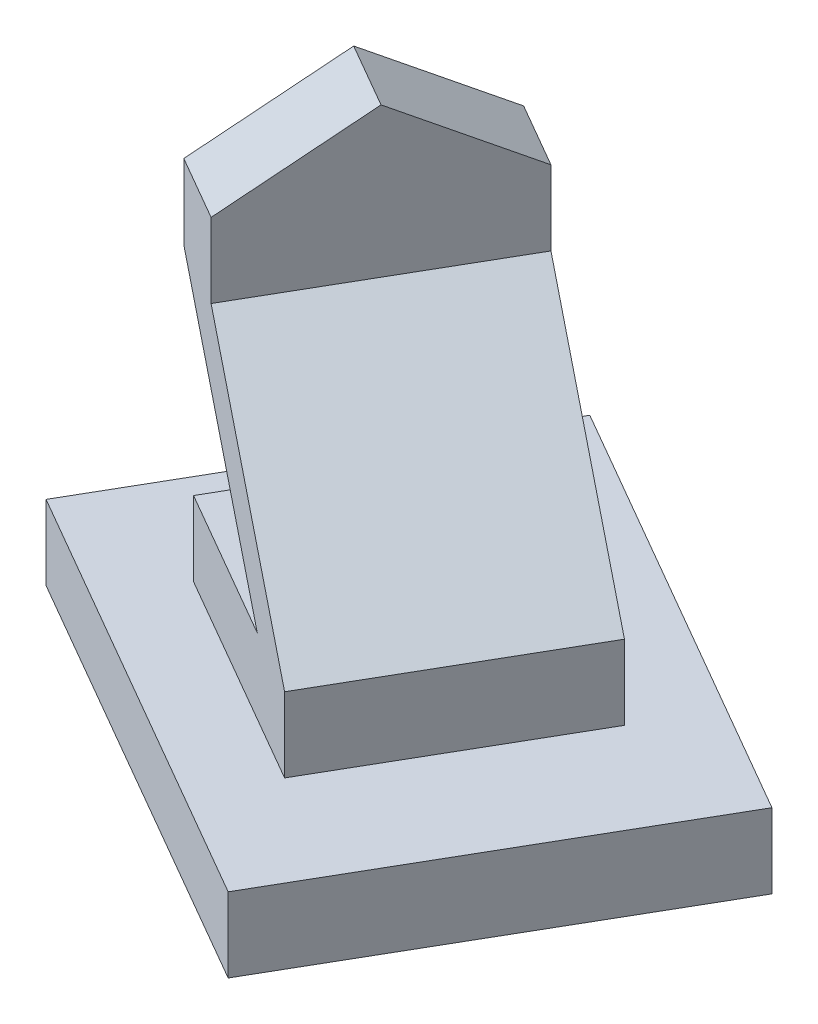
SolidWorks part; units mm, degrees
other "Perspective"
ref_plane "Front" through (0, 0, 0) normal (0, 0, 1) x (1, 0, 0)
ref_plane "Top" through (0, 0, 0) normal (0, 1, 0) x (1, 0, 0)
ref_plane "Right" through (0, 0, 0) normal (1, 0, 0) x (0, 0, -1)
sketch "Sketch1" plane through (0, 0, 0) normal (0, 1, 0) x (1, 0, 0)
  line L0 (0, 0) -> (800, 1385.6406)
  line L1 (800, 1385.6406) -> (-932.0508, 2385.6406)
  line L2 (-932.0508, 2385.6406) -> (-1732.0508, 1000)
  line L3 (-1732.0508, 1000) -> (0, 0)
  line L4 (0, 0) -> (48.1177, 0) construction
  dimension "D1" = 60
  dimension "D2" = 2000
  dimension "D3" = 1600
extrude "Extrude1" add sketch "Sketch1" along normal blind 300
sketch "Sketch2" plane through (0, 300, 0) normal (0, 1, 0) x (-1, 0, 0)
  line L0 (649.0381, -1875.833) -> (-216.9873, -1375.833)
  line L1 (-216.9873, -1375.833) -> (283.0127, -509.8076)
  line L2 (283.0127, -509.8076) -> (1149.0381, -1009.8076)
  line L3 (1149.0381, -1009.8076) -> (649.0381, -1875.833)
  line L4 (1732.0508, -1000) -> (0, 0) construction
  line L5 (932.0508, -2385.6406) -> (1732.0508, -1000) construction
  line L6 (0, 0) -> (-800, -1385.6406) construction
  line L7 (-800, -1385.6406) -> (932.0508, -2385.6406) construction
  dimension "D1" = 500
  dimension "D2" = 500
  dimension "D3" = 300
  dimension "D4" = 300
extrude "Extrude2" add sketch "Sketch2" along normal blind 300
sketch "Sketch3" plane through (150, 0, -259.8076) normal (-0.5, 0, 0.866) x (0.866, 0, 0.5)
  line L0 (-500, 600) -> (-1307.2736, 1400)
  line L1 (-1307.2736, 1400) -> (-1307.2736, 1700)
  line L2 (-1307.2736, 1700) -> (-1607.2736, 1700)
  line L3 (-1607.2736, 1700) -> (-1607.2736, 1400)
  line L4 (-1607.2736, 1400) -> (-800, 600)
  line L5 (-1500, 600) -> (-500, 600) construction
  line L6 (-800, 600) -> (-500, 600)
  dimension "D1" = 300
  dimension "D2" = 300
  dimension "D3" = 800
  dimension "D4" = 300
  dimension "D5" = 300
extrude "Extrude3" add sketch "Sketch3" against normal blind 1000
sketch "Sketch4" plane through (-1132.1321, 0, -653.6368) normal (0.866, 0, 0.5) x (0.5, 0, -0.866)
  line L0 (300, 1700) -> (1300, 1700)
  line L1 (1300, 1700) -> (800, 2000)
  line L2 (800, 2000) -> (300, 1700)
  dimension "D1" = 300
extrude "Extrude4" add sketch "Sketch4" against normal blind 300
